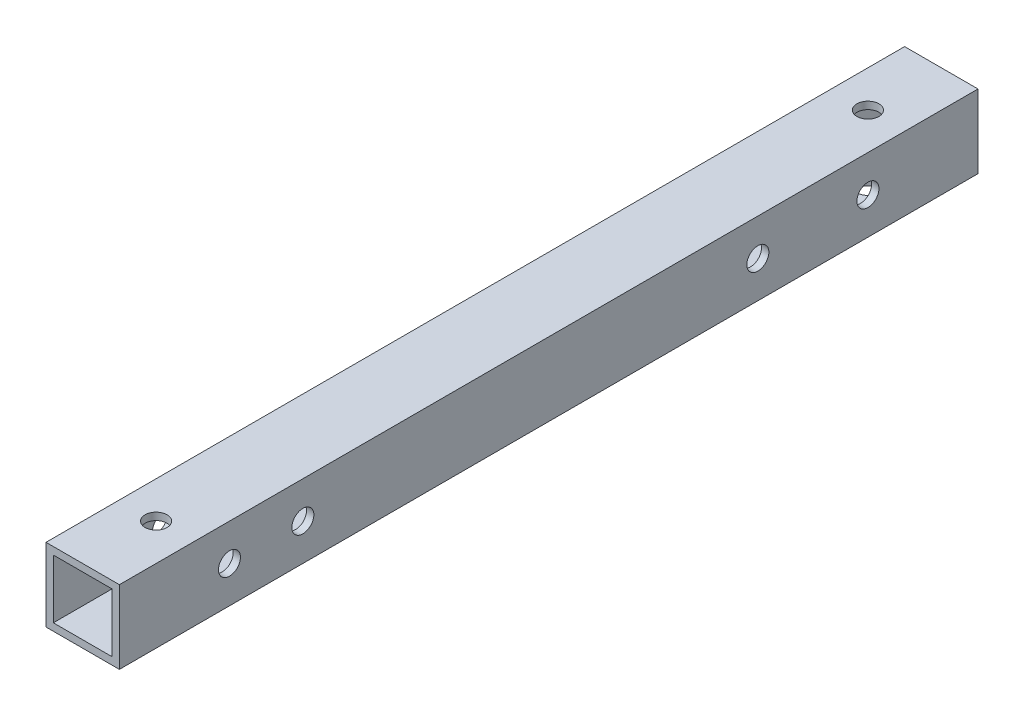
SolidWorks part; units mm, degrees
material "6063-O"
ref_plane "前视基准面" through (0, 0, 0) normal (0, 0, 1) x (1, 0, 0)
ref_plane "上视基准面" through (0, 0, 0) normal (0, 1, 0) x (1, 0, 0)
ref_plane "右视基准面" through (0, 0, 0) normal (1, 0, 0) x (0, 0, -1)
other "Configuration Table"
sketch "草图1" plane through (0, 0, 0) normal (0, 0, 1) x (1, 0, 0)
  line L1 (-5, 5) -> (5, 5)
  line L2 (-5, 5) -> (-5, -5)
  line L3 (-5, -5) -> (5, -5)
  line L4 (5, 5) -> (5, -5)
  line L5 (-5, 5) -> (5, -5) construction
  line L6 (-5, -5) -> (5, 5) construction
  point P4 (0, 0)
  dimension "D1" = 10
  dimension "D2" = 10
extrude "拉伸-薄壁1" add sketch "草图1" along normal blind 117 thin
sketch "草图2" plane through (0, 5, 0) normal (0, 1, 0) x (1, 0, 0)
  line L0 (0, -117) -> (0, 0) construction
  line L1 (5, -117) -> (-5, -117) construction
  line L2 (5, 0) -> (-5, 0) construction
  line L3 (5, -58.5) -> (-5, -58.5) construction
  line L4 (5, -117) -> (5, 0) construction
  line L5 (-5, -117) -> (-5, 0) construction
  circle A0 centre (0, -10) radius 1.5
  circle A1 centre (0, -25) radius 1.5 construction
  circle A2 centre (0, -107) radius 1.5
  circle A3 centre (0, -92) radius 1.5 construction
  circle A4 centre (0, -76.7) radius 1.5 construction
  dimension "D1" = 3
  dimension "D2" = 10
  dimension "D3" = 15
  dimension "D4" = 40.3
  dimension "D5" = 10
extrude "切除-拉伸1" cut sketch "草图2" against normal through all
sketch "草图3" plane through (5, 0, 0) normal (1, 0, 0) x (0, 0, -1)
  line L0 (0, 0) -> (-117, 0) construction
  line L1 (0, -5) -> (0, 5) construction
  line L2 (-117, -5) -> (-117, 5) construction
  circle A0 centre (-15, 0) radius 1.5
  circle A1 centre (-30, 0) radius 1.5
  circle A2 centre (-102, 0) radius 1.5
  circle A3 centre (-92, 0) radius 1.5
  dimension "D1" = 3
  dimension "D2" = 15
  dimension "D3" = 15
  dimension "D4" = 10
  dimension "D5" = 15
extrude "切除-拉伸2" cut sketch "草图3" against normal blind 10
